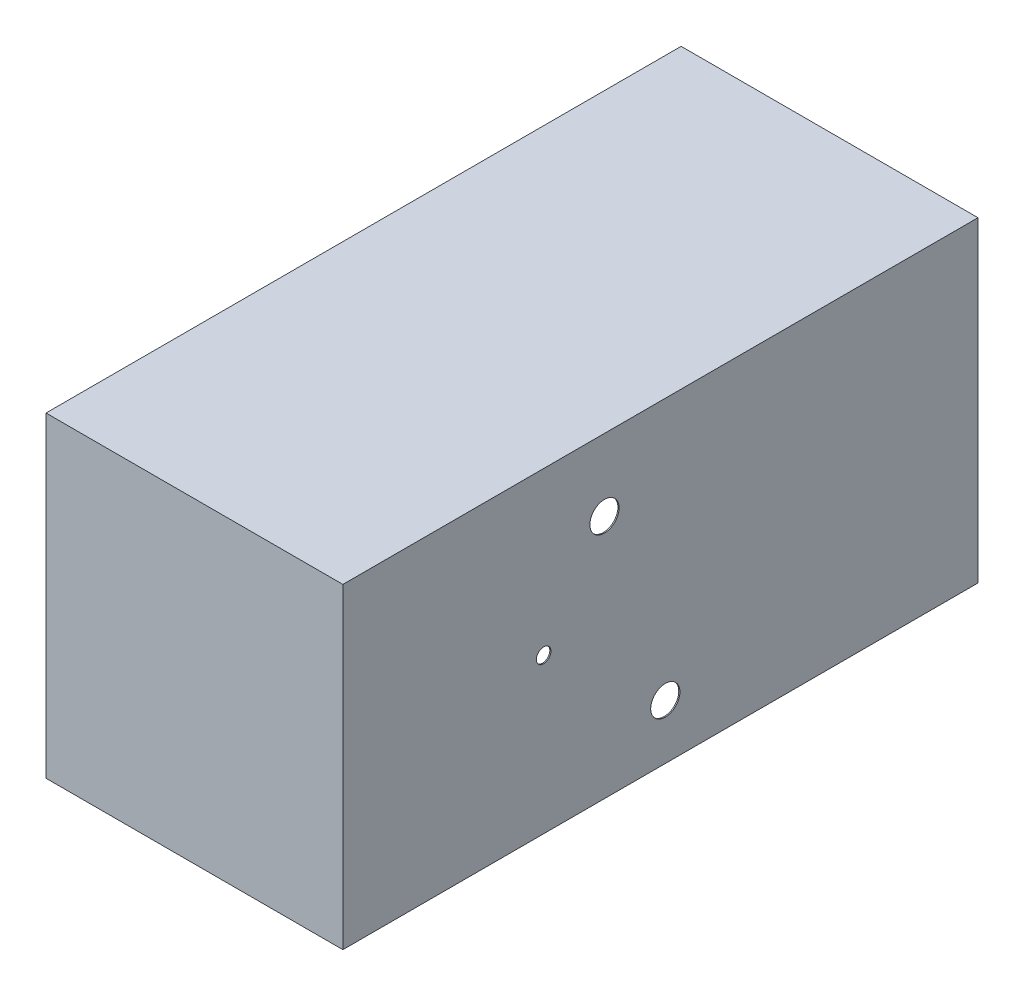
SolidWorks part; units mm, degrees
ref_plane "Plano frontal" through (0, 0, 0) normal (0, 0, 1) x (1, 0, 0)
ref_plane "Plano superior" through (0, 0, 0) normal (0, 1, 0) x (1, 0, 0)
ref_plane "Plano direito" through (0, 0, 0) normal (1, 0, 0) x (0, 0, -1)
sketch "Sketch3" plane through (0, 0, 0) normal (0, 1, 0) x (1, 0, 0)
  line L1 (305, 652.5) -> (-305, 652.5)
  line L2 (305, 652.5) -> (305, -652.5)
  line L3 (305, -652.5) -> (-305, -652.5)
  line L4 (-305, 652.5) -> (-305, -652.5)
  line L5 (305, 652.5) -> (-305, -652.5) construction
  line L6 (305, -652.5) -> (-305, 652.5) construction
  line L7 (302.6628, 647.5) -> (-302.6628, 647.5)
  line L8 (302.6628, 647.5) -> (302.6628, -647.5)
  line L9 (302.6628, -647.5) -> (-302.6628, -647.5)
  line L10 (-302.6628, 647.5) -> (-302.6628, -647.5)
  line L11 (302.6628, 647.5) -> (-302.6628, -647.5) construction
  line L12 (302.6628, -647.5) -> (-302.6628, 647.5) construction
  point P0 (0, 0)
  point P6 (0, 0)
  dimension "D1" = 1305
  dimension "D2" = 610
  dimension "D3" = 5
extrude "Boss-Extrude2" add sketch "Sketch3" along normal blind 640 contours L1 L4 L3 L2 L10 L7 L8 L9
sketch "Sketch4" plane through (305, 0, 0) normal (1, 0, 0) x (0, 0, -1)
  line L0 (652.5, 317.5) -> (-240, 317.5) construction
  line L1 (652.5, 640) -> (652.5, 0) construction
  line L2 (-240, 317.5) -> (-240, 0) construction
  line L3 (652.5, 0) -> (-652.5, 0) construction
  line L4 (652.5, 502.5) -> (-115, 502.5) construction
  line L5 (-115, 502.5) -> (-115, 0) construction
  line L6 (652.5, 112.5) -> (10, 112.5) construction
  line L7 (10, 112.5) -> (10, 0) construction
  circle A0 centre (-115, 502.5) radius 30
  circle A1 centre (10, 112.5) radius 30
  circle A2 centre (-240, 317.5) radius 15
  dimension "D7" = 60
  dimension "D8" = 30
  dimension "D1" = 767.5
  dimension "D2" = 892.5
  dimension "D3" = 642.5
  dimension "D4" = 112.5
  dimension "D5" = 317.5
  dimension "D6" = 502.5
extrude "Cut-Extrude1" cut sketch "Sketch4" against normal blind 640
sketch "Sketch5" plane through (0, 640, 0) normal (0, 1, 0) x (1, 0, 0)
  line L1 (305, 652.5) -> (-305, 652.5)
  line L2 (305, 652.5) -> (305, -652.5)
  line L3 (305, -652.5) -> (-305, -652.5)
  line L4 (-305, 652.5) -> (-305, -652.5)
  line L5 (305, 652.5) -> (-305, -652.5) construction
  line L6 (305, -652.5) -> (-305, 652.5) construction
  point P0 (0, 0)
extrude "Boss-Extrude3" add sketch "Sketch5" along normal blind 10
sketch "Sketch6" plane through (305, 0, 0) normal (1, 0, 0) x (0, 0, -1)
  line L0 (602.5, 489.9051) -> (652.5, 489.9051) construction
  line L1 (152.5, 600) -> (602.5, 600)
  line L2 (152.5, 600) -> (152.5, 50)
  line L3 (152.5, 50) -> (602.5, 50)
  line L4 (602.5, 600) -> (602.5, 50)
  line L5 (152.5, 600) -> (602.5, 50) construction
  line L6 (152.5, 50) -> (602.5, 600) construction
  line L7 (652.5, 650) -> (652.5, 0) construction
  line L8 (415.3633, 600) -> (415.3633, 650) construction
  line L9 (-652.5, 650) -> (652.5, 650) construction
  line L10 (463.2705, 50) -> (463.2705, 0) construction
  line L11 (652.5, 0) -> (-652.5, 0) construction
  point P0 (377.5, 325)
  dimension "D1" = 450
  dimension "D2" = 550
extrude "Cut-Extrude2" [suppressed] cut sketch "Sketch6" against normal blind 1298
